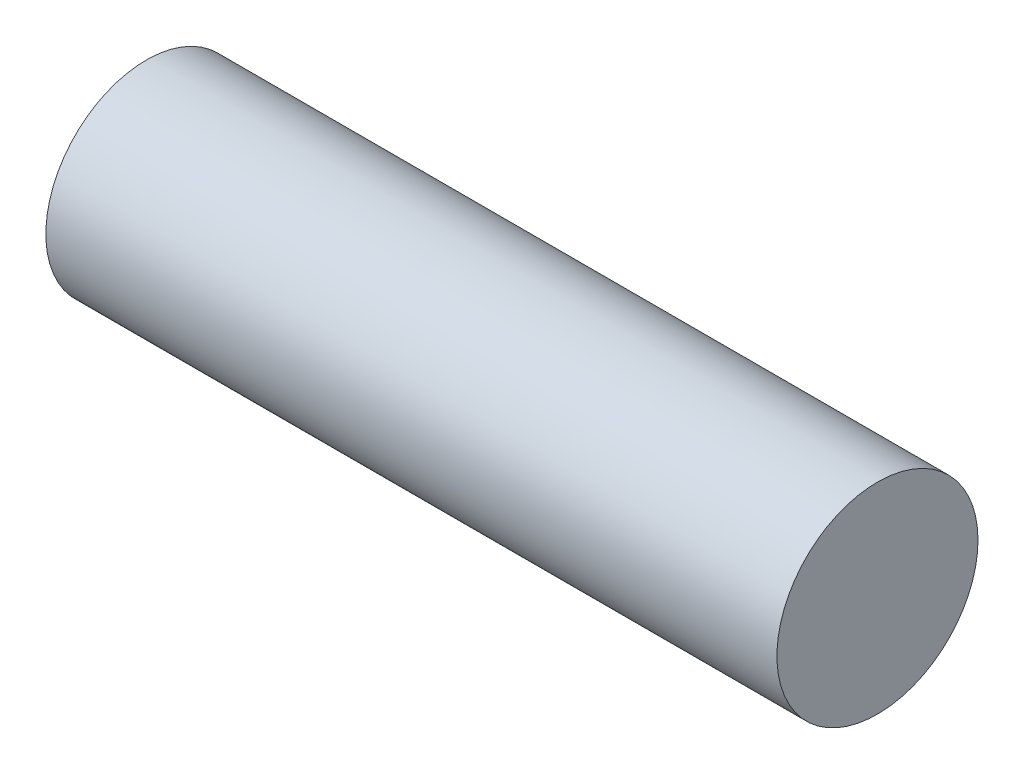
SolidWorks part; units mm, degrees
ref_plane "Front Plane" through (0, 0, 0) normal (0, 0, 1) x (1, 0, 0)
ref_plane "Top Plane" through (0, 0, 0) normal (0, 1, 0) x (1, 0, 0)
ref_plane "Right Plane" through (0, 0, 0) normal (1, 0, 0) x (0, 0, -1)
sketch "Sketch1" plane through (0, 0, 0) normal (1, 0, 0) x (0, 0, -1)
  circle A0 centre (0, 0) radius 55
  dimension "D1" = 110
extrude "Boss-Extrude1" add sketch "Sketch1" along normal blind 400
